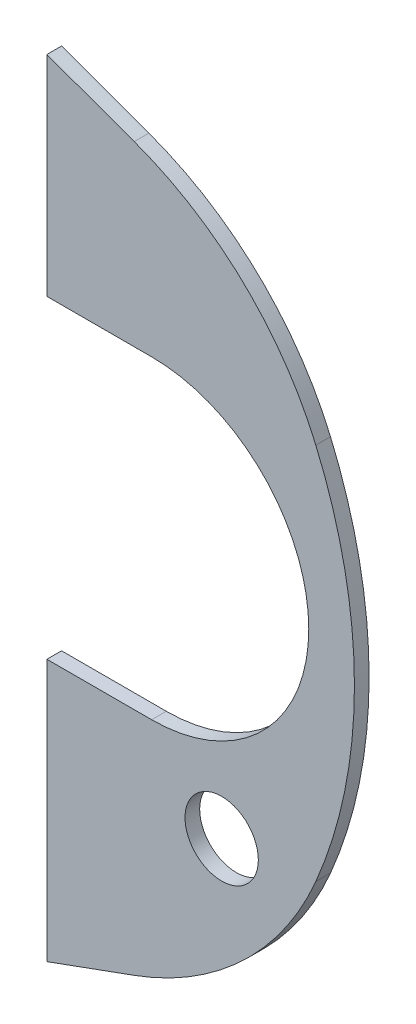
SolidWorks part; units mm, degrees
ref_plane "Front Plane" through (0, 0, 0) normal (0, 0, 1) x (1, 0, 0)
ref_plane "Top Plane" through (0, 0, 0) normal (0, 1, 0) x (1, 0, 0)
ref_plane "Right Plane" through (0, 0, 0) normal (1, 0, 0) x (0, 0, -1)
sketch "Sketch1" plane through (0, 0, 0) normal (0, 0, 1) x (1, 0, 0)
  line L1 (0, 0) -> (5, 0)
  line L2 (0, 0) -> (0, 12.5)
  line L3 (0, 12.5) -> (5, 12.5)
  line L4 (5, 0) -> (5, 12.5) construction
  line L5 (0, 27.5) -> (5, 27.5)
  line L6 (0, 27.5) -> (0, 37.5)
  line L7 (0, 37.5) -> (5, 37.5)
  line L8 (5, 27.5) -> (5, 37.5) construction
  arc A0 (5, 37.5) -> (5, 0) centre (-8.3206, 18.75) cw
  arc A1 (5, 27.5) -> (5, 12.5) centre (5, 20) cw
  dimension "D5" = 23
  dimension "D1" = 12.5
  dimension "D2" = 10
  dimension "D3" = 15
  dimension "D4" = 5
extrude "Boss-Extrude1" add sketch "Sketch1" along normal blind 0.7
sketch "Sketch2" plane through (0, 0, 0.7) normal (0, 0, 1) x (1, 0, 0)
  line L0 (0, 37.5) -> (13.3749, 32.6319)
  line L1 (0, 0) -> (14.6459, 5.3307)
  line L2 (0, 0) -> (5, 0) construction
  line L3 (5, 37.5) -> (0, 37.5) construction
  line L4 (0, 37.5) -> (10.5451, 37.5)
  line L5 (10.5451, 37.5) -> (13.3749, 32.6319)
  line L6 (0, 0) -> (11.6819, 0)
  line L7 (11.6819, 0) -> (14.6459, 5.3307)
  circle A0 centre (8.342, 9.2526) radius 1.75
  dimension "D3" = 3.5
  dimension "D1" = 20
  dimension "D2" = 20
extrude "Cut-Extrude1" cut sketch "Sketch2" against normal blind 10
fillet "Fillet1" radius 15 2 edges at (8.5426, 34.3907, 0.35) (8.5426, 3.1093, 0.35)
